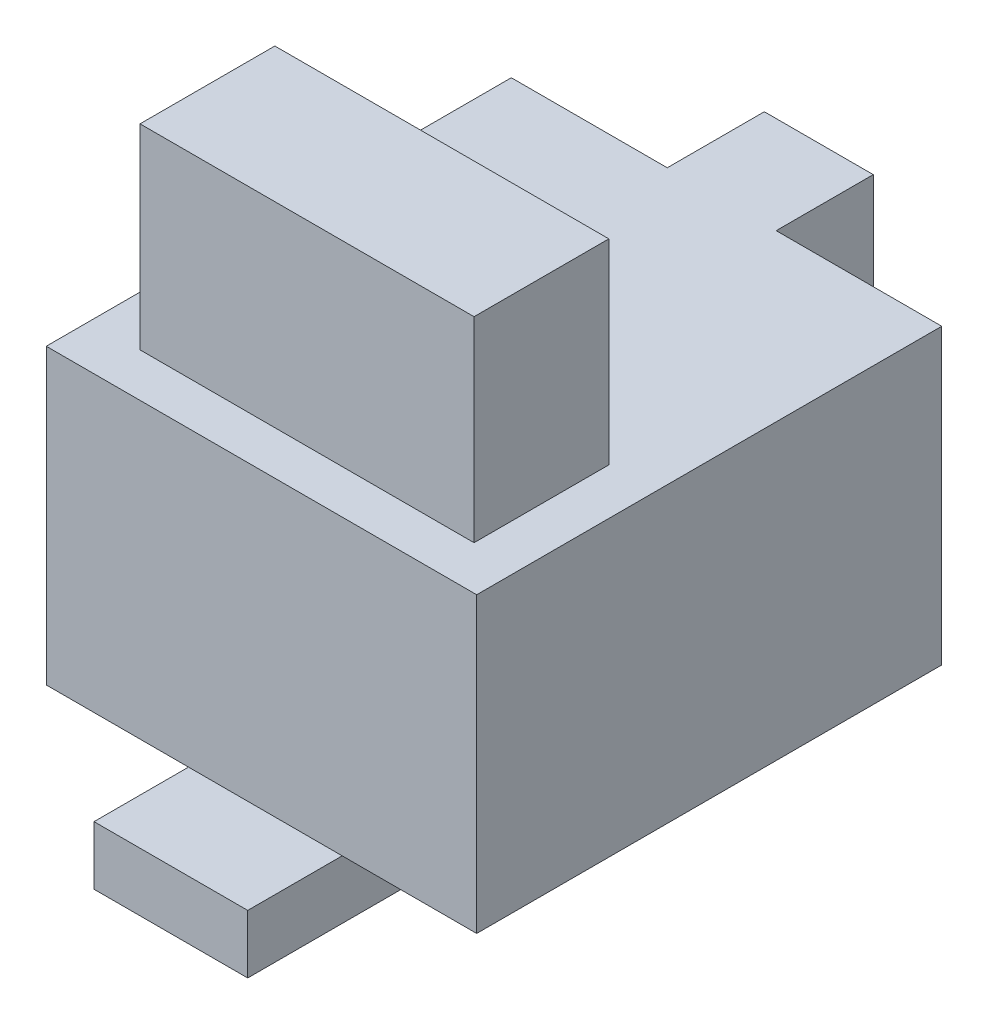
SolidWorks part; units mm, degrees
ref_plane "Front Plane" through (0, 0, 0) normal (0, 0, 1) x (1, 0, 0)
ref_plane "Top Plane" through (0, 0, 0) normal (0, 1, 0) x (1, 0, 0)
ref_plane "Right Plane" through (0, 0, 0) normal (1, 0, 0) x (0, 0, -1)
sketch "Sketch1" plane through (0, 0, 0) normal (0, 1, 0) x (1, 0, 0)
  line L1 (19.955, 21.56) -> (-19.955, 21.56)
  line L2 (19.955, 21.56) -> (19.955, -21.56)
  line L3 (19.955, -21.56) -> (-19.955, -21.56)
  line L4 (-19.955, 21.56) -> (-19.955, -21.56)
  line L5 (19.955, 21.56) -> (-19.955, -21.56) construction
  line L6 (19.955, -21.56) -> (-19.955, 21.56) construction
  point P0 (0, 0)
  dimension "D1" = 39.91
  dimension "D2" = 43.12
extrude "Boss-Extrude1" add sketch "Sketch1" along normal blind 27.2
sketch "Sketch2" plane through (0, 0, -21.56) normal (0, 0, -1) x (-1, 0, 0)
  line L0 (-19.955, 27.2) -> (19.955, 27.2) construction
  line L1 (5.495, 27.2) -> (-4.605, 27.2)
  line L2 (5.495, 27.2) -> (5.495, 12.07)
  line L3 (5.495, 12.07) -> (-4.605, 12.07)
  line L4 (-4.605, 27.2) -> (-4.605, 12.07)
  line L5 (19.955, 27.2) -> (19.955, 0) construction
  dimension "D1" = 15.13
  dimension "D2" = 10.1
  dimension "D3" = 14.46
extrude "Boss-Extrude2" add sketch "Sketch2" along normal blind 9
sketch "Sketch5" plane through (0, 0, 0) normal (0, -1, 0) x (1, 0, 0)
  line L0 (19.955, 21.56) -> (19.955, -21.56) construction
  line L1 (7.485, 15.7) -> (-6.765, 15.7)
  line L2 (7.485, 15.7) -> (7.485, 30.32)
  line L3 (7.485, 30.32) -> (-6.765, 30.32)
  line L4 (-6.765, 15.7) -> (-6.765, 30.32)
  line L5 (-19.955, 21.56) -> (19.955, 21.56) construction
  dimension "D1" = 14.25
  dimension "D2" = 14.62
  dimension "D3" = 12.47
  dimension "D4" = 8.76
extrude "Boss-Extrude3" add sketch "Sketch5" along normal blind 5.43
sketch "Sketch6" plane through (0, 27.2, 0) normal (0, 1, 0) x (1, 0, 0)
  line L1 (-15.315, -5.0046) -> (15.655, -5.0046)
  line L2 (-15.315, -5.0046) -> (-15.315, -17.5046)
  line L3 (-15.315, -17.5046) -> (15.655, -17.5046)
  line L4 (15.655, -5.0046) -> (15.655, -17.5046)
  line L5 (19.955, -21.56) -> (19.955, 21.56) construction
  point P8 (-80.71, -45.0342)
  point P9 (-80.6138, -43.0852)
  dimension "D1" = 12.5
  dimension "D2" = 30.97
  dimension "D4" = 4.3
extrude "Boss-Extrude4" add sketch "Sketch6" along normal blind 18.15
